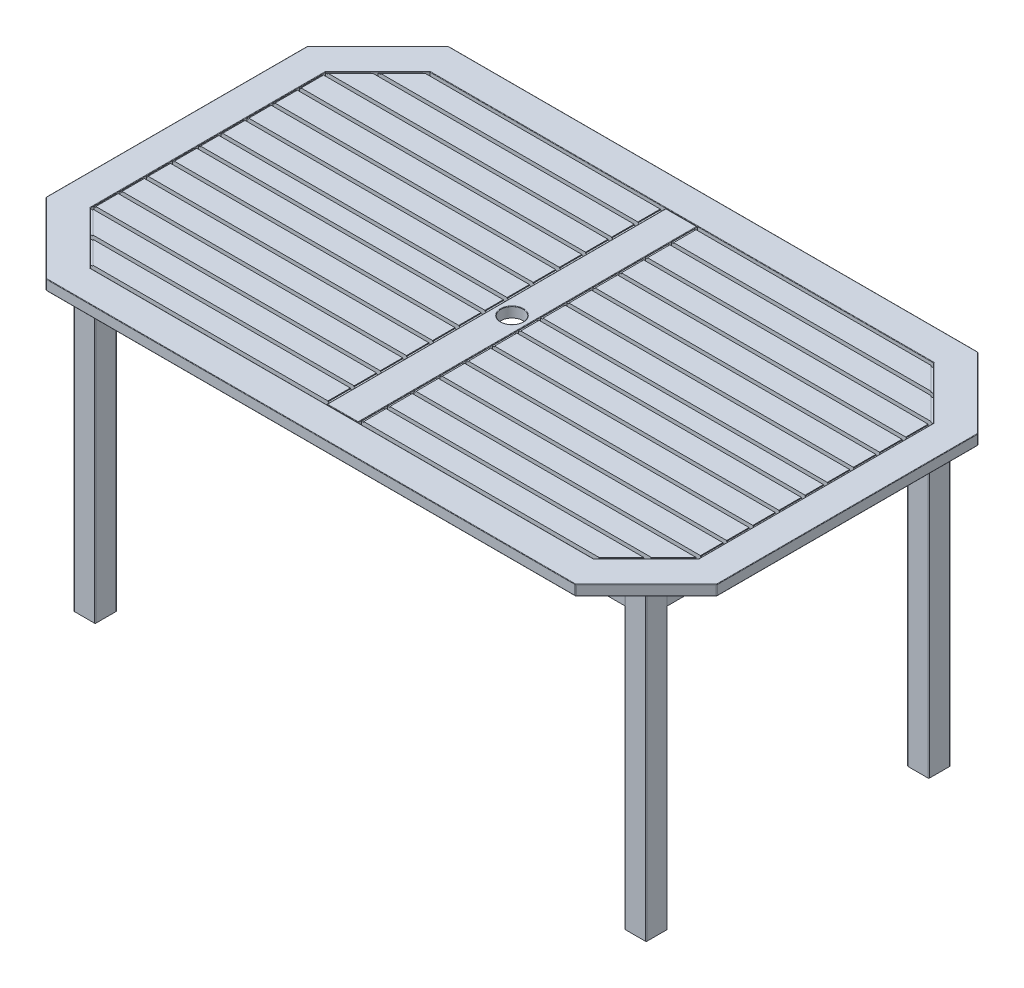
SolidWorks part; units mm, degrees
material "Teck"
ref_plane "Plan de face" through (0, 0, 0) normal (0, 0, 1) x (1, 0, 0)
ref_plane "Plan de dessus" through (0, 0, 0) normal (0, 1, 0) x (1, 0, 0)
ref_plane "Plan de droite" through (0, 0, 0) normal (1, 0, 0) x (0, 0, -1)
sketch "Esquisse1" plane through (0, 0, 0) normal (0, 1, 0) x (1, 0, 0)
  line L0 (-592, 292) -> (592, 292) construction
  line L1 (-638.5, 340) -> (-593.5, 340)
  line L2 (-640, 338.5) -> (-640, 293.5)
  line L3 (-638.5, 292) -> (-593.5, 292)
  line L4 (-592, 338.5) -> (-592, 293.5)
  line L5 (593.5, 292) -> (638.5, 292)
  line L6 (592, 293.5) -> (592, 338.5)
  line L7 (593.5, 340) -> (638.5, 340)
  line L8 (640, 293.5) -> (640, 338.5)
  line L9 (638.5, -292) -> (593.5, -292)
  line L10 (640, -293.5) -> (640, -338.5)
  line L11 (638.5, -340) -> (593.5, -340)
  line L12 (592, -293.5) -> (592, -338.5)
  line L13 (-593.5, -340) -> (-638.5, -340)
  line L14 (-592, -338.5) -> (-592, -293.5)
  line L15 (-593.5, -292) -> (-638.5, -292)
  line L16 (-640, -338.5) -> (-640, -293.5)
  line L17 (592, -292) -> (-592, -292) construction
  line L18 (0, -292) -> (0, 292) construction
  arc A0 (640, -338.5) -> (638.5, -340) centre (638.5, -338.5) cw
  arc A1 (638.5, 292) -> (640, 293.5) centre (638.5, 293.5) ccw
  arc A2 (638.5, 340) -> (640, 338.5) centre (638.5, 338.5) cw
  arc A3 (592, 338.5) -> (593.5, 340) centre (593.5, 338.5) cw
  arc A4 (593.5, 292) -> (592, 293.5) centre (593.5, 293.5) cw
  arc A5 (638.5, -292) -> (640, -293.5) centre (638.5, -293.5) cw
  arc A6 (593.5, -292) -> (592, -293.5) centre (593.5, -293.5) ccw
  arc A7 (593.5, -340) -> (592, -338.5) centre (593.5, -338.5) cw
  arc A8 (-638.5, -340) -> (-640, -338.5) centre (-638.5, -338.5) cw
  arc A9 (-593.5, -340) -> (-592, -338.5) centre (-593.5, -338.5) ccw
  arc A10 (-592, -293.5) -> (-593.5, -292) centre (-593.5, -293.5) ccw
  arc A11 (-638.5, -292) -> (-640, -293.5) centre (-638.5, -293.5) ccw
  arc A12 (-593.5, 292) -> (-592, 293.5) centre (-593.5, 293.5) ccw
  arc A13 (-640, 293.5) -> (-638.5, 292) centre (-638.5, 293.5) ccw
  arc A14 (-638.5, 340) -> (-640, 338.5) centre (-638.5, 338.5) ccw
  arc A15 (-593.5, 340) -> (-592, 338.5) centre (-593.5, 338.5) cw
  point P53 (-640, 340)
  point P56 (-592, 340)
  dimension "D2" = 1.5
  dimension "D1" = 48
  dimension "D3" = 1280
  dimension "D4" = 680
extrude "Boss.-Extru.1" add sketch "Esquisse1" against normal blind 700
sketch "Esquisse3" plane through (0, 0, 0) normal (0, 1, 0) x (1, 0, 0)
  line L0 (-592, 450) -> (592, 450)
  line L1 (592, 450) -> (750, 292)
  line L2 (750, 292) -> (750, -292)
  line L3 (750, -292) -> (592, -450)
  line L4 (592, -450) -> (-592, -450)
  line L5 (-592, -450) -> (-750, -292)
  line L6 (-750, -292) -> (-750, 292)
  line L7 (-750, 292) -> (-592, 450)
  line L8 (-750, 292) -> (750, 292) construction
  line L9 (-750, -292) -> (750, -292) construction
  line L10 (-592, 450) -> (592, -450) construction
  line L11 (-592, 450) -> (-592, -450) construction
  line L12 (592, 450) -> (592, -450) construction
  line L13 (592, 450) -> (-592, -450) construction
  line L14 (593.5, 292) -> (638.5, 292) construction
  line L15 (-563.0051, 380) -> (-35, 380)
  line L16 (563.0051, 380) -> (680, 263.0051)
  line L17 (680, 263.0051) -> (680, -263.0051)
  line L18 (680, -263.0051) -> (563.0051, -380)
  line L19 (563.0051, -380) -> (35, -380)
  line L20 (-563.0051, -380) -> (-680, -263.0051)
  line L21 (-680, -263.0051) -> (-680, 263.0051)
  line L22 (-680, 263.0051) -> (-563.0051, 380)
  line L23 (-35, 380) -> (-35, -380)
  line L24 (-35, -380) -> (35, 380) construction
  line L25 (35, 380) -> (35, -380)
  line L26 (35, 380) -> (563.0051, 380)
  line L27 (-35, -380) -> (-563.0051, -380)
  line L28 (-563.0051, 380) -> (563.0051, 380) construction
  line L29 (-35, 380) -> (35, 380) construction
  line L30 (563.0051, -380) -> (-563.0051, -380) construction
  line L31 (-35, -380) -> (35, -380) construction
  line L32 (-750, 0) -> (-680, 0) construction
  circle A0 centre (0, 0) radius 25
  dimension "D4" = 50
  dimension "D1" = 900
  dimension "D2" = 1500
  dimension "D3" = 70
extrude "Boss.-Extru.4" add sketch "Esquisse3" along normal blind 23
sketch "Esquisse4" plane through (0, 0, 0) normal (0, 1, 0) x (1, 0, 0)
  line L0 (-592, 293.5) -> (-592, 338.5) construction
  line L1 (-592, 338.5) -> (592, 338.5)
  line L2 (-592, 338.5) -> (-592, 315.5)
  line L3 (-592, 315.5) -> (592, 315.5)
  line L4 (592, 338.5) -> (592, 315.5)
  line L5 (592, 338.5) -> (592, 293.5) construction
  line L6 (593.5, 292) -> (638.5, 292) construction
  line L7 (638.5, 292) -> (615.5, 292)
  line L8 (638.5, 292) -> (638.5, -292)
  line L9 (638.5, -292) -> (615.5, -292)
  line L10 (615.5, 292) -> (615.5, -292)
  line L11 (638.5, -292) -> (593.5, -292) construction
  line L12 (592, -293.5) -> (592, -338.5) construction
  line L13 (592, -338.5) -> (-592, -338.5)
  line L14 (592, -338.5) -> (592, -315.5)
  line L15 (592, -315.5) -> (-592, -315.5)
  line L16 (-592, -338.5) -> (-592, -315.5)
  line L17 (-592, -338.5) -> (-592, -293.5) construction
  line L18 (-593.5, -292) -> (-638.5, -292) construction
  line L19 (-638.5, -292) -> (-615.5, -292)
  line L20 (-638.5, -292) -> (-638.5, 292)
  line L21 (-638.5, 292) -> (-615.5, 292)
  line L22 (-615.5, -292) -> (-615.5, 292)
  line L23 (-638.5, 292) -> (-593.5, 292) construction
  dimension "D1" = 23
extrude "Boss.-Extru.6" add sketch "Esquisse4" against normal blind 75
sketch "Esquisse5" plane through (0, 0, 0) normal (0, 1, 0) x (1, 0, 0)
  line L1 (-35, 380) -> (-563.0051, 380) construction
  line L2 (-530, 380) -> (-480, 380)
  line L3 (-530, 380) -> (-530, -380)
  line L4 (-530, -380) -> (-480, -380)
  line L5 (-480, 380) -> (-480, -380)
  line L7 (-563.0051, -380) -> (-35, -380) construction
  line L8 (563.0051, 380) -> (35, 380) construction
  line L9 (480, 380) -> (530, 380)
  line L10 (480, 380) -> (480, -380)
  line L11 (480, -380) -> (530, -380)
  line L12 (530, 380) -> (530, -380)
  line L16 (35, -380) -> (563.0051, -380) construction
  line L18 (-680, 263.0051) -> (-680, -263.0051) construction
  line L19 (-480, 0) -> (0, 0) construction
  line L21 (0, 0) -> (480, 0) construction
  dimension "D1" = 50
  dimension "D2" = 150
extrude "Boss.-Extru.7" add sketch "Esquisse5" along normal blind 12 separate body
sketch "Esquisse6" plane through (0, 23, 0) normal (0, 1, 0) x (1, 0, 0)
  line L0 (-571.5025, 371.5025) -> (-35, 371.5025)
  line L1 (-563.0051, 380) -> (-680, 263.0051) construction
  line L2 (-35, -380) -> (-35, 380) construction
  line L3 (-35, 371.5025) -> (-35, 321.5025)
  line L4 (-35, 315.5) -> (-35, 338.5) construction
  line L5 (-35, 321.5025) -> (-621.5025, 321.5025)
  line L6 (-621.5025, 321.5025) -> (-571.5025, 371.5025)
  line L7 (-630, 313.0051) -> (-35, 313.0051)
  line L8 (-35, 313.0051) -> (-35, 263.0051)
  line L9 (-35, 263.0051) -> (-680, 263.0051)
  line L10 (-680, 263.0051) -> (-630, 313.0051)
  line L11 (-35, 380) -> (-35, 371.5025) construction
  line L12 (-35, 321.5025) -> (-35, 313.0051) construction
  line L13 (-25, 0) -> (25, 0) construction
  line L14 (-680, 263.0051) -> (-680, -263.0051) construction
  line L15 (-680, 254.5076) -> (-35, 254.5076)
  line L16 (-680, 254.5076) -> (-680, 204.5076)
  line L17 (-680, 204.5076) -> (-35, 204.5076)
  line L18 (-35, 254.5076) -> (-35, 204.5076)
  line L19 (-35, 263.0051) -> (-35, 254.5076) construction
  line L20 (-35, 196.0101) -> (-680, 196.0101)
  line L21 (-35, 196.0101) -> (-35, 146.0101)
  line L22 (-35, 146.0101) -> (-680, 146.0101)
  line L23 (-680, 196.0101) -> (-680, 146.0101)
  line L24 (-680, 137.5126) -> (-35, 137.5126)
  line L25 (-680, 137.5126) -> (-680, 87.5126)
  line L26 (-680, 87.5126) -> (-35, 87.5126)
  line L27 (-35, 137.5126) -> (-35, 87.5126)
  line L28 (-35, 79.0152) -> (-680, 79.0152)
  line L29 (-35, 79.0152) -> (-35, 29.0152)
  line L30 (-35, 29.0152) -> (-680, 29.0152)
  line L31 (-680, 79.0152) -> (-680, 29.0152)
  line L32 (-35, 204.5076) -> (-35, 196.0101) construction
  line L33 (-35, 196.0101) -> (-34.6337, 196.1551) construction
  line L34 (-35, 146.0101) -> (-35, 137.5126) construction
  line L35 (-35, 137.5126) -> (-35, 146.0101) construction
  line L36 (-35, 87.5126) -> (-35, 79.0152) construction
  line L37 (-35, 29.0152) -> (-35, 20.5177) construction
  line L38 (-35, 20.5177) -> (-680, 20.5177)
  line L39 (0, 25) -> (0, -25) construction
  line L40 (35, 29.0152) -> (35, 20.5177) construction
  line L41 (35, 87.5126) -> (35, 79.0152) construction
  line L42 (35, 137.5126) -> (35, 146.0101) construction
  line L43 (35, 146.0101) -> (35, 137.5126) construction
  line L44 (35, 196.0101) -> (34.6337, 196.1551) construction
  line L45 (35, 204.5076) -> (35, 196.0101) construction
  line L46 (35, 263.0051) -> (35, 254.5076) construction
  line L47 (35, 321.5025) -> (35, 313.0051) construction
  line L48 (35, 380) -> (35, 371.5025) construction
  line L49 (35, 20.5177) -> (680, 20.5177)
  line L50 (680, 79.0152) -> (680, 29.0152)
  line L51 (35, 29.0152) -> (680, 29.0152)
  line L52 (35, 79.0152) -> (35, 29.0152)
  line L53 (35, 79.0152) -> (680, 79.0152)
  line L54 (35, 137.5126) -> (35, 87.5126)
  line L55 (680, 87.5126) -> (35, 87.5126)
  line L56 (680, 137.5126) -> (680, 87.5126)
  line L57 (680, 137.5126) -> (35, 137.5126)
  line L58 (680, 196.0101) -> (680, 146.0101)
  line L59 (35, 146.0101) -> (680, 146.0101)
  line L60 (35, 196.0101) -> (35, 146.0101)
  line L61 (35, 196.0101) -> (680, 196.0101)
  line L62 (35, 254.5076) -> (35, 204.5076)
  line L63 (680, 204.5076) -> (35, 204.5076)
  line L64 (680, 254.5076) -> (680, 204.5076)
  line L65 (680, 254.5076) -> (35, 254.5076)
  line L66 (680, 263.0051) -> (630, 313.0051)
  line L67 (35, 263.0051) -> (680, 263.0051)
  line L68 (35, 313.0051) -> (35, 263.0051)
  line L69 (630, 313.0051) -> (35, 313.0051)
  line L70 (621.5025, 321.5025) -> (571.5025, 371.5025)
  line L71 (35, 321.5025) -> (621.5025, 321.5025)
  line L72 (35, 371.5025) -> (35, 321.5025)
  line L73 (571.5025, 371.5025) -> (35, 371.5025)
  line L74 (35, -380) -> (35, -371.5025) construction
  line L75 (35, -321.5025) -> (35, -313.0051) construction
  line L76 (35, -263.0051) -> (35, -254.5076) construction
  line L77 (35, -204.5076) -> (35, -196.0101) construction
  line L78 (35, -196.0101) -> (34.6337, -196.1551) construction
  line L79 (35, -146.0101) -> (35, -137.5126) construction
  line L80 (35, -137.5126) -> (35, -146.0101) construction
  line L81 (35, -87.5126) -> (35, -79.0152) construction
  line L82 (35, -29.0152) -> (35, -20.5177) construction
  line L83 (-35, -29.0152) -> (-35, -20.5177) construction
  line L84 (-35, -87.5126) -> (-35, -79.0152) construction
  line L85 (-35, -137.5126) -> (-35, -146.0101) construction
  line L86 (-35, -146.0101) -> (-35, -137.5126) construction
  line L87 (-35, -196.0101) -> (-34.6337, -196.1551) construction
  line L88 (-35, -204.5076) -> (-35, -196.0101) construction
  line L89 (-35, -263.0051) -> (-35, -254.5076) construction
  line L90 (-35, -321.5025) -> (-35, -313.0051) construction
  line L91 (-35, -380) -> (-35, -371.5025) construction
  line L92 (571.5025, -371.5025) -> (35, -371.5025)
  line L93 (35, -371.5025) -> (35, -321.5025)
  line L94 (35, -321.5025) -> (621.5025, -321.5025)
  line L95 (621.5025, -321.5025) -> (571.5025, -371.5025)
  line L96 (630, -313.0051) -> (35, -313.0051)
  line L97 (35, -313.0051) -> (35, -263.0051)
  line L98 (35, -263.0051) -> (680, -263.0051)
  line L99 (680, -263.0051) -> (630, -313.0051)
  line L100 (680, -254.5076) -> (35, -254.5076)
  line L101 (680, -254.5076) -> (680, -204.5076)
  line L102 (680, -204.5076) -> (35, -204.5076)
  line L103 (35, -254.5076) -> (35, -204.5076)
  line L104 (35, -196.0101) -> (680, -196.0101)
  line L105 (35, -196.0101) -> (35, -146.0101)
  line L106 (35, -146.0101) -> (680, -146.0101)
  line L107 (680, -196.0101) -> (680, -146.0101)
  line L108 (680, -137.5126) -> (35, -137.5126)
  line L109 (680, -137.5126) -> (680, -87.5126)
  line L110 (680, -87.5126) -> (35, -87.5126)
  line L111 (35, -137.5126) -> (35, -87.5126)
  line L112 (35, -79.0152) -> (680, -79.0152)
  line L113 (35, -79.0152) -> (35, -29.0152)
  line L114 (35, -29.0152) -> (680, -29.0152)
  line L115 (680, -79.0152) -> (680, -29.0152)
  line L116 (35, -20.5177) -> (680, -20.5177)
  line L117 (-35, -20.5177) -> (-680, -20.5177)
  line L118 (-680, -79.0152) -> (-680, -29.0152)
  line L119 (-35, -29.0152) -> (-680, -29.0152)
  line L120 (-35, -79.0152) -> (-35, -29.0152)
  line L121 (-35, -79.0152) -> (-680, -79.0152)
  line L122 (-35, -137.5126) -> (-35, -87.5126)
  line L123 (-680, -87.5126) -> (-35, -87.5126)
  line L124 (-680, -137.5126) -> (-680, -87.5126)
  line L125 (-680, -137.5126) -> (-35, -137.5126)
  line L126 (-680, -196.0101) -> (-680, -146.0101)
  line L127 (-35, -146.0101) -> (-680, -146.0101)
  line L128 (-35, -196.0101) -> (-35, -146.0101)
  line L129 (-35, -196.0101) -> (-680, -196.0101)
  line L130 (-35, -254.5076) -> (-35, -204.5076)
  line L131 (-680, -204.5076) -> (-35, -204.5076)
  line L132 (-680, -254.5076) -> (-680, -204.5076)
  line L133 (-680, -254.5076) -> (-35, -254.5076)
  line L134 (-680, -263.0051) -> (-630, -313.0051)
  line L135 (-35, -263.0051) -> (-680, -263.0051)
  line L136 (-35, -313.0051) -> (-35, -263.0051)
  line L137 (-630, -313.0051) -> (-35, -313.0051)
  line L138 (-621.5025, -321.5025) -> (-571.5025, -371.5025)
  line L139 (-35, -321.5025) -> (-621.5025, -321.5025)
  line L140 (-35, -371.5025) -> (-35, -321.5025)
  line L141 (-571.5025, -371.5025) -> (-35, -371.5025)
  line L142 (-680, 20.5177) -> (-680, -20.5177)
  line L143 (-35, 20.5177) -> (-35, -20.5177)
  line L144 (35, 20.5177) -> (35, -20.5177)
  line L145 (680, 20.5177) -> (680, -20.5177)
  circle A0 centre (0, 0) radius 25 construction
extrude "Boss.-Extru.8" add sketch "Esquisse6" against normal up to surface (11 mm away) up to face at (505, 12, 0)
sketch "Esquisse7" plane through (0, 23, 0) normal (0, 1, 0) x (1, 0, 0)
  line L0 (-563.0051, 380) -> (-680, 263.0051)
  line L1 (-680, 263.0051) -> (-680, -263.0051)
  line L2 (-680, -263.0051) -> (-563.0051, -380)
  line L3 (-563.0051, -380) -> (563.0051, -380)
  line L4 (563.0051, -380) -> (680, -263.0051)
  line L5 (680, -263.0051) -> (680, 263.0051)
  line L6 (680, 263.0051) -> (563.0051, 380)
  line L7 (563.0051, 380) -> (-563.0051, 380)
  line L8 (561.3482, 376) -> (40, 376)
  line L9 (-561.3482, 376) -> (-676, 261.3482)
  line L10 (-676, 261.3482) -> (-676, -261.3482)
  line L11 (-676, -261.3482) -> (-561.3482, -376)
  line L12 (-561.3482, -376) -> (-40, -376)
  line L13 (561.3482, -376) -> (676, -261.3482)
  line L14 (676, -261.3482) -> (676, 261.3482)
  line L15 (676, 261.3482) -> (561.3482, 376)
  line L16 (-35, 379) -> (-35, -376)
  line L18 (-35, -263.0051) -> (-35, -254.5076) construction
  line L19 (35, -376) -> (35, 379)
  line L20 (35, 321.5025) -> (35, 313.0051) construction
  line L21 (-40, 376) -> (-561.3482, 376)
  line L22 (40, -376) -> (561.3482, -376)
  line L23 (561.3482, 376) -> (-561.3482, 376) construction
  line L24 (-40, 376) -> (-40, -376)
  line L25 (-561.3482, -376) -> (561.3482, -376) construction
  line L26 (40, -376) -> (40, 376)
  line L27 (35, -376) -> (35, 376) construction
  line L29 (35, 380) -> (35, 371.5025) construction
  line L30 (-35, 376) -> (-35, -376) construction
  line L31 (-35, 371.5025) -> (-35, 380) construction
  line L32 (-35, 379) -> (35, 379)
  line L33 (35, 379) -> (35.1427, 379.0945)
  line L35 (-35, -376) -> (-35, -379)
  line L36 (-35, -380) -> (-35, -371.5025) construction
  line L37 (-35, -379) -> (35, -379)
  line L38 (35, -371.5025) -> (35, -380) construction
  line L39 (35, -379) -> (35, -376)
  dimension "D4" = 1
  dimension "D5" = 1
  dimension "D1" = 4
  dimension "D2" = 5
  dimension "D3" = 5
extrude "Enlèv. mat.-Extru.1" cut sketch "Esquisse7" against normal blind 2
fillet "Congé1" radius 4 8 edges at (750, 11.5, -292) (592, 11.5, -450) (-592, 11.5, -450) (-750, 11.5, -292) (-750, 11.5, 292) (-592, 11.5, 450) (750, 11.5, 292) (592, 11.5, 450)
fillet "Congé2" radius 1 45 edges at (0, 23, -379) (0, 23, 379) (671, 0, -371) (671, 23, -371) (-671, 0, -371) (0, 0, -450) (750, 0, 0) (671, 0, 371) (0, 0, 450) (-671, 0, 371) (-750, 0, 0) (591.8739, 0, 449.6955) (749.6955, 0, 291.8739) (-591.8739, 0, 449.6955) (-749.6955, 0, 291.8739) (-749.6955, 0, -291.8739) (-591.8739, 0, -449.6955) (591.8739, 0, -449.6955) (749.6955, 0, -291.8739) (750, 23, 0) (-671, 23, -371) (-750, 23, 0) (-671, 23, 371) (0, 23, 450) (671, 23, 371) (0, 23, -450) (591.8739, 23, 449.6955) (749.6955, 23, 291.8739) (-591.8739, 23, 449.6955) (-749.6955, 23, 291.8739) (-749.6955, 23, -291.8739) (-591.8739, 23, -449.6955) (591.8739, 23, -449.6955) (749.6955, 23, -291.8739) (-35, 23, 0) (35, 23, 0) (-621.5025, 23, -321.5025) (-680, 23, 0) (621.5025, 23, -321.5025) (0, 23, 380) (0, 23, -380) (621.5025, 23, 321.5025) (680, 23, 0) (0, 23, 25) (-621.5025, 23, 321.5025)
